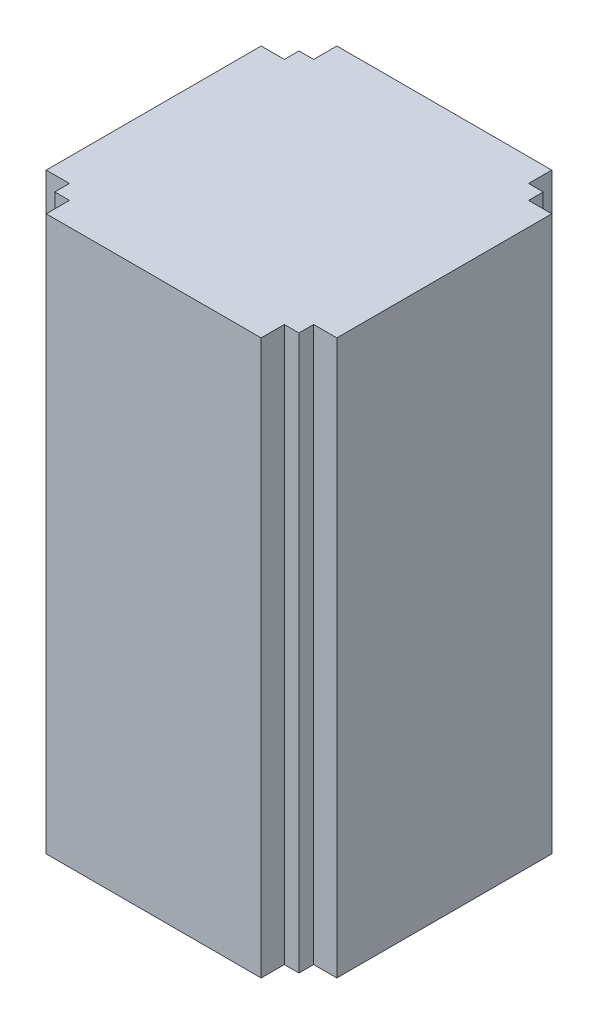
SolidWorks part; units mm, degrees
ref_plane "Front Plane" through (0, 0, 0) normal (0, 0, 1) x (1, 0, 0)
ref_plane "Top Plane" through (0, 0, 0) normal (0, 1, 0) x (1, 0, 0)
ref_plane "Right Plane" through (0, 0, 0) normal (1, 0, 0) x (0, 0, -1)
sketch "Sketch1" plane through (0, 0, 0) normal (0, 1, 0) x (1, 0, 0)
  line L0 (-44, 50) -> (-44, 59.5)
  line L1 (-50, -50) -> (-44, -50)
  line L2 (-50, -50) -> (-50, -44)
  line L3 (-50, 50) -> (-44, 50)
  line L4 (50, -50) -> (50, -44)
  line L5 (-50, -50) -> (50, 50) construction
  line L6 (-50, 50) -> (50, -50) construction
  line L7 (-59.5, -44) -> (-50, -44)
  line L8 (-59.5, -44) -> (-59.5, 44)
  line L9 (-59.5, 44) -> (-50, 44)
  line L10 (59.5, -44) -> (59.5, 44)
  line L11 (-59.5, -44) -> (59.5, 44) construction
  line L12 (-59.5, 44) -> (59.5, -44) construction
  line L13 (-44, -59.5) -> (44, -59.5)
  line L14 (-44, -59.5) -> (-44, -50)
  line L15 (-44, 59.5) -> (44, 59.5)
  line L16 (44, -59.5) -> (44, -50)
  line L17 (-44, -59.5) -> (44, 59.5) construction
  line L18 (-44, 59.5) -> (44, -59.5) construction
  line L19 (50, 44) -> (59.5, 44)
  line L20 (-50, 44) -> (-50, 50)
  line L21 (44, 50) -> (50, 50)
  line L22 (44, 50) -> (44, 59.5)
  line L23 (50, 44) -> (50, 50)
  line L24 (50, -44) -> (59.5, -44)
  line L25 (44, -50) -> (50, -50)
  point P0 (0, 0)
  point P6 (0, 0)
  point P11 (0, 0)
  dimension "D1" = 100
  dimension "D2" = 100
  dimension "D3" = 88
  dimension "D4" = 88
  dimension "D5" = 119
  dimension "D6" = 119
extrude "Boss-Extrude1" add sketch "Sketch1" along normal blind 227
